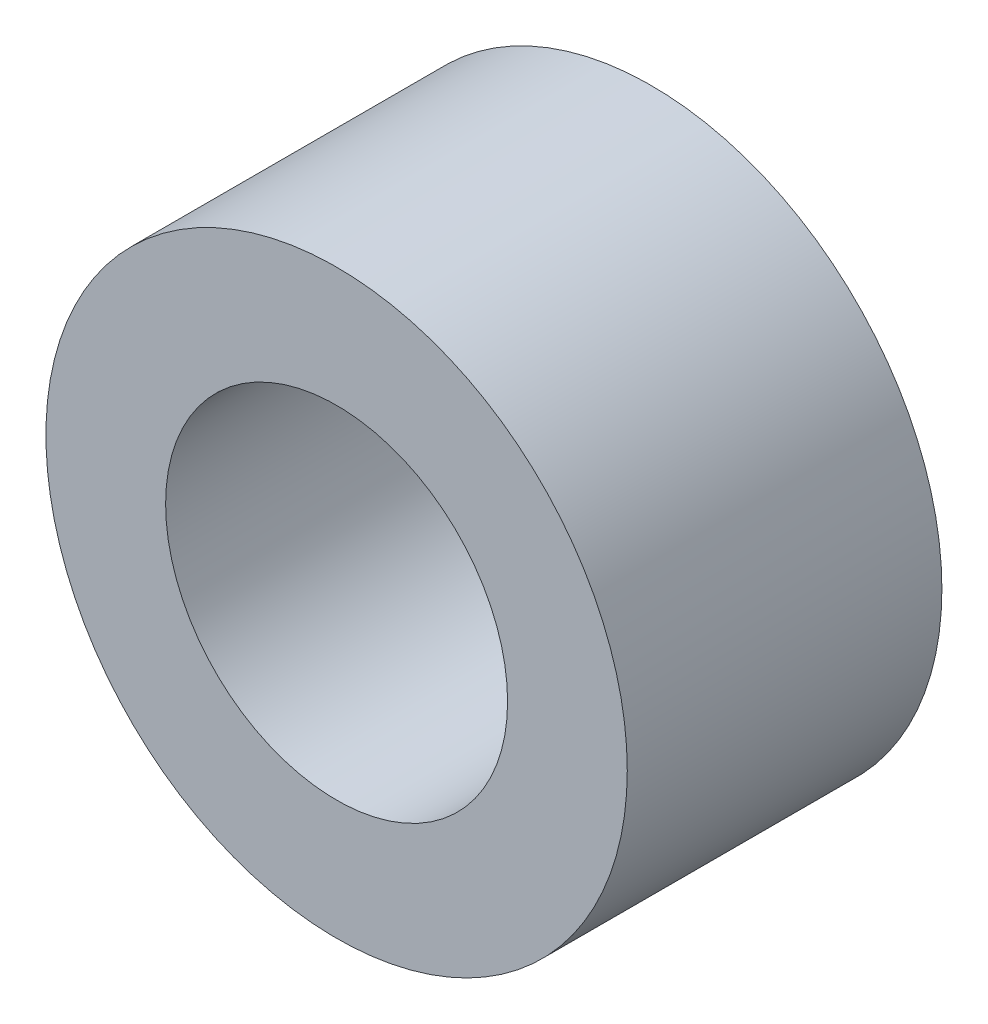
SolidWorks part; units mm, degrees
ref_plane "前视基准面" through (0, 0, 0) normal (0, 0, 1) x (1, 0, 0)
ref_plane "上视基准面" through (0, 0, 0) normal (0, 1, 0) x (1, 0, 0)
ref_plane "右视基准面" through (0, 0, 0) normal (1, 0, 0) x (0, 0, -1)
sketch "草图3" plane through (0, 0, 0) normal (0, 0, 1) x (1, 0, 0)
  circle A0 centre (0, 0) radius 8.5
extrude "凸台-拉伸2" add sketch "草图3" along normal mid plane 9.2
sketch "草图4" plane through (0, 0, 0) normal (0, 0, 1) x (1, 0, 0)
  circle A0 centre (0, 0) radius 5
extrude "切除-拉伸1" cut sketch "草图4" against normal mid plane 9.2
